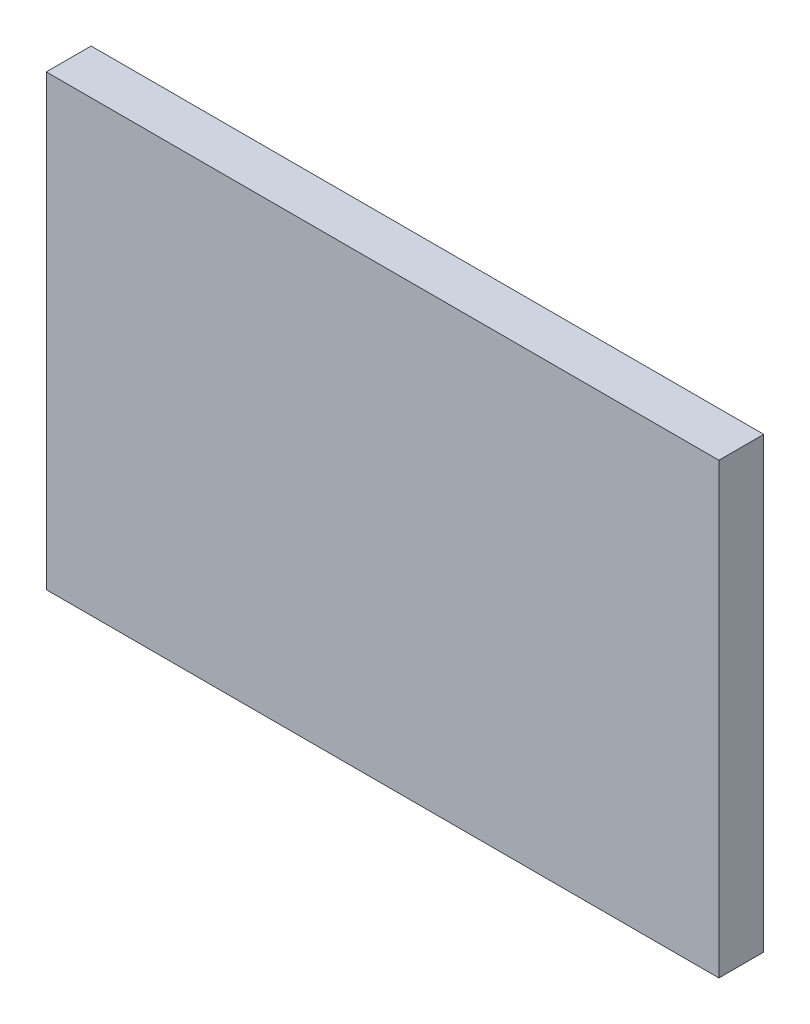
SolidWorks part; units mm, degrees
material "Полиуретановый жесткий пенопласт"
ref_plane "Спереди" through (0, 0, 0) normal (0, 0, 1) x (1, 0, 0)
ref_plane "Сверху" through (0, 0, 0) normal (0, 1, 0) x (1, 0, 0)
ref_plane "Справа" through (0, 0, 0) normal (1, 0, 0) x (0, 0, -1)
sketch "Эскиз1" plane through (0, 0, 0) normal (0, 0, 1) x (1, 0, 0)
  line L1 (75, -50) -> (-75, -50)
  line L2 (75, -50) -> (75, 50)
  line L3 (75, 50) -> (-75, 50)
  line L4 (-75, -50) -> (-75, 50)
  line L5 (75, -50) -> (-75, 50) construction
  line L6 (75, 50) -> (-75, -50) construction
  point P0 (0, 0)
  dimension "D1" = 150
  dimension "D2" = 100
extrude "Бобышка-Вытянуть1" add sketch "Эскиз1" along normal blind 10
